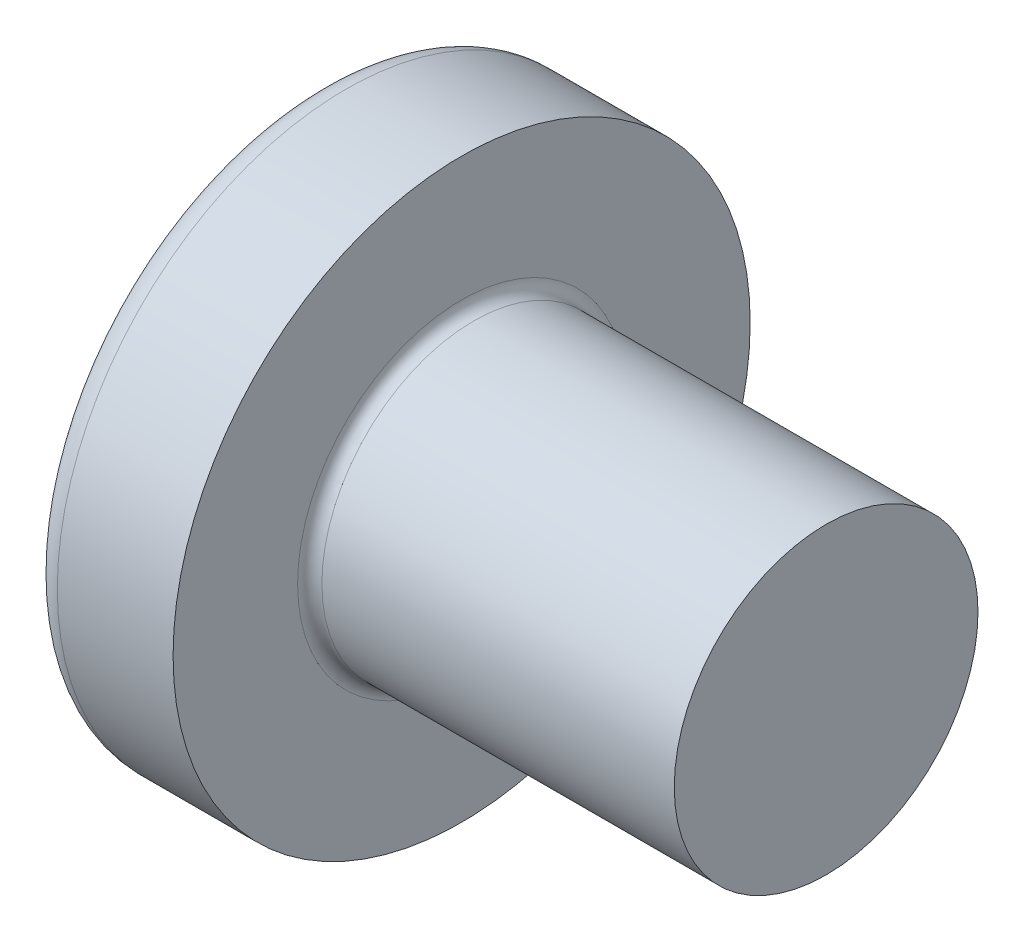
SolidWorks part; units mm, degrees
ref_plane "Plane1" through (0, 0, 0) normal (0, 0, 1) x (1, 0, 0)
ref_plane "Plane2" through (0, 0, 0) normal (0, 1, 0) x (1, 0, 0)
ref_plane "Plane3" through (0, 0, 0) normal (1, 0, 0) x (0, 0, -1)
sketch "BodySke" plane through (0, 0, 0) normal (0, 0, 1) x (1, 0, 0)
  line L0 (3.7, 2.5) -> (3.7, 4.75)
  line L1 (4.1, 6.35) -> (4.1, -3.175) construction
  line L2 (-25.4, 0) -> (127, 0) construction
  line L3 (9.7, 0) -> (0, 0)
  line L4 (3.7, 2.5) -> (9.7, 2.5)
  line L5 (9.7, 2.5) -> (9.7, 0)
  line L6 (1.7942, 4.75) -> (3.7, 4.75)
  line L8 (3.7, 6.35) -> (3.7, -3.175) construction
  arc A0 (1.4243, 4.5563) -> (0, 0) centre (8, 0) ccw
  arc A2 (1.4243, 4.5563) -> (1.7942, 4.75) centre (1.7942, 4.3) cw
  dimension "Head_fillet_rad" = 0.45
  dimension "Head_crown_rad" = 8
  dimension "Head_ht" = 3.7
  dimension "Diameter" = 5
  dimension "Length" = 6
  dimension "Head_dia" = 9.5
  dimension "Advance" = 0.8
  dimension "Thread_nom" = 6
revolve "Base-Revolve" add sketch "BodySke"
cosmetic thread "ThreadCosmetic" [suppressed]
fillet "Fillet1" radius 0.2 1 edges at (3.7, 0, 2.5)
sketch "Sketch3" plane through (0, 0, 0) normal (1, 0, 0) x (0, 0, -1)
  line L0 (0.515, -2.35) -> (-0.515, -2.35)
  line L1 (0.515, -2.35) -> (0.515, 2.35)
  line L2 (-0.515, 2.35) -> (0.515, 2.35)
  line L3 (-0.515, 2.35) -> (-0.515, -2.35)
  dimension "D1" = 2.35
  dimension "Cross_dia" = 4.7
  dimension "D2" = 0.515
  dimension "Cross_width" = 1.03
ref_plane "Plane4" through (2.74, 0, 0) normal (1, 0, 0) x (0, 0, -1)
sketch "Sketch4" plane through (2.74, 0, 0) normal (1, 0, 0) x (0, 0, -1)
  line L0 (0.515, -0.9839) -> (-0.515, -0.9839)
  line L1 (0.515, -0.9839) -> (0.515, 0.9839)
  line L2 (-0.515, 0.9839) -> (0.515, 0.9839)
  line L3 (-0.515, 0.9839) -> (-0.515, -0.9839)
  dimension "D1" = 1.03
  dimension "D2" = 1.9678
  dimension "D3" = 0.515
  dimension "D4" = 0.9839
loft "Recess" cut profiles "Sketch3", "Sketch4"
pattern_circular "RecPat" count 2 every 90 about axis through (0, 0, 0) along (1, 0, 0) of "Recess"
sketch "RecCorSke" plane through (0, 0, 0) normal (0, 0, 1) x (1, 0, 0)
  line L0 (-3.175, 0) -> (15.875, 0) construction
  line L1 (-25.4, 0) -> (127, 0) construction
  line L2 (0, 0) -> (0, 1.0426)
  line L3 (0, 1.0426) -> (2.74, 0.851)
  line L4 (2.74, 0.851) -> (3.0165, 0)
  line L5 (3.0165, 0) -> (0, 0)
  dimension "Diameter" = 1.702
  dimension "Depth" = 2.74
  dimension "Draft_angle" = 4
  dimension "Bottom_angle" = 18
revolve "RecessCore" cut sketch "RecCorSke" angle 360 about L0
sketch "ThdSchSke" [suppressed] plane through (0, 0, 0) normal (0, 0, 1) x (1, 0, 0)
  line L0 (10.5, -4.172) -> (9.9202, -5)
  line L1 (10.5, -4.172) -> (11.0798, -5)
  line L2 (11.0798, -5) -> (11.0798, -6.25)
  line L3 (-3.175, 0) -> (5.1513, 0) construction
  line L5 (11.0798, -6.25) -> (9.9202, -6.25)
  line L6 (9.9202, -6.25) -> (9.9202, -5)
  dimension "Thread_minor" = 4.11
  dimension "Diameter" = 5
  dimension "Start" = 5.3
  dimension "SideAngle" = 55
  dimension "VeeAngle" = 70
  dimension "Overcut" = 6.25
revolve "ThreadSchematic" [suppressed] cut sketch "ThdSchSke" angle 360 about L3
pattern_linear "ThdSchPat" [suppressed]
equation "\"D1@Sketch3\" = \"Cross_dia@Sketch3\" / 2"
equation "\"D2@Sketch3\" = \"Cross_width@Sketch3\" / 2"
equation "\"Depth@RecCorSke\" = \"Cross_depth@Plane4\""
equation "\"D1@Sketch4\" = \"Cross_width@Sketch3\""
equation "\"D2@Sketch4\" = \"Cross_dia@Sketch3\" - 2.0 * \"Cross_depth@Plane4\" * tan(26.5  * 0.017453292)"
equation "\"D3@Sketch4\" = \"D1@Sketch4\" / 2"
equation "\"D4@Sketch4\" = \"D2@Sketch4\" / 2"
equation "\"Thread_length@ThreadCosmetic\" = ((sgn( (\"Length@BodySke\" - \"Advance@BodySke\" * 2.0 ) - \"Thread_nom@BodySke\" )-1)*( (\"Length@BodySke\" - \"Advance@BodySke\" * 2.0 ) - \"Thread_nom@BodySke\" ))/-2+ \"Thread_nom@BodySke\""
equation "\"Thread_minor@ThdSchSke\" = \"Thread_minor@ThreadCosmetic\""
equation "\"Diameter@ThdSchSke\" = \"Diameter@BodySke\""
equation "\"Overcut@ThdSchSke\" = \"Diameter@BodySke\" * 1.25"
equation "\"Start@ThdSchSke\" = \"Head_ht@BodySke\" + \"Length@BodySke\" - \"Thread_length@ThreadCosmetic\"  '---Non-countersunk---"
equation "\"Num_threads@ThdSchPat\" = int( \"Thread_length@ThreadCosmetic\" / \"Advance@BodySke\" + 0.999 )  + 1"
equation "\"Advance@ThdSchPat\" = \"Thread_length@ThreadCosmetic\" /  (\"Num_threads@ThdSchPat\" - 1) 'relax it"
